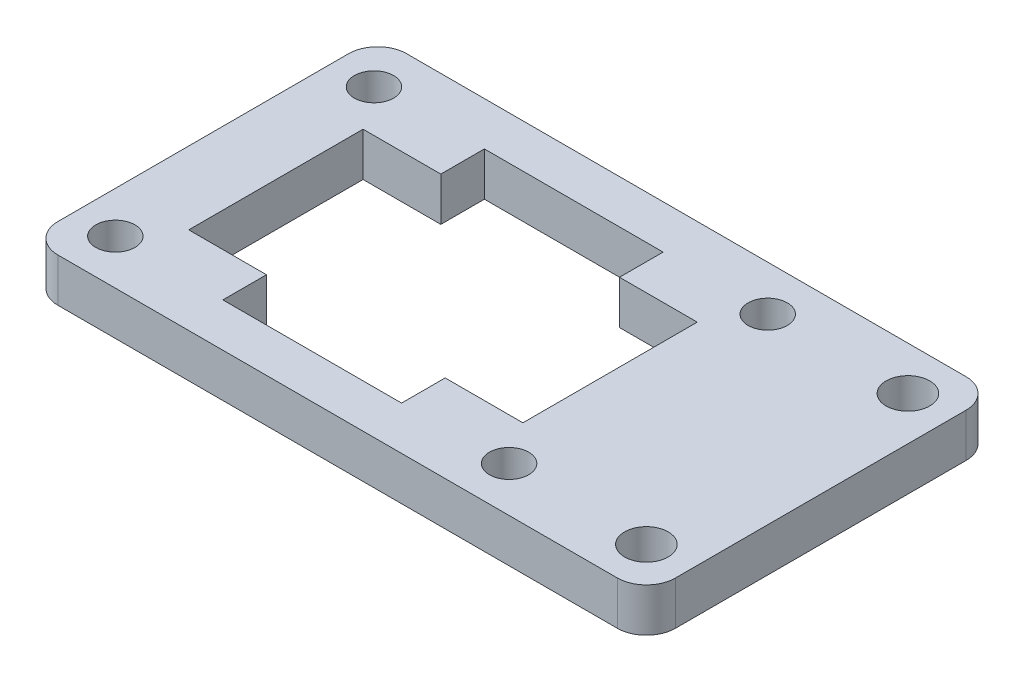
SolidWorks part; units mm, degrees
ref_plane "Front Plane" through (0, 0, 0) normal (0, 0, 1) x (1, 0, 0)
ref_plane "Top Plane" through (0, 0, 0) normal (0, 1, 0) x (1, 0, 0)
ref_plane "Right Plane" through (0, 0, 0) normal (1, 0, 0) x (0, 0, -1)
sketch "Sketch1" plane through (0, 0, 0) normal (0, 1, 0) x (1, 0, 0)
  line L0 (16.5, 21) -> (16.5, 18) construction
  line L1 (0, 0) -> (42.5, 0)
  line L2 (0, 0) -> (0, 24)
  line L3 (0, 24) -> (42.5, 24)
  line L4 (42.5, 0) -> (42.5, 24)
  line L5 (5, 18) -> (28, 18)
  line L6 (5, 18) -> (5, 6)
  line L7 (5, 6) -> (28, 6)
  line L8 (28, 18) -> (28, 6)
  line L9 (10.5, 18) -> (22.5, 18)
  line L10 (10.5, 18) -> (10.5, 21)
  line L11 (10.5, 21) -> (22.5, 21)
  line L12 (22.5, 18) -> (22.5, 21)
  line L13 (10.5, 6) -> (22.5, 6)
  line L14 (10.5, 6) -> (10.5, 3)
  line L15 (10.5, 3) -> (22.5, 3)
  line L16 (22.5, 6) -> (22.5, 3)
  circle A0 centre (2.85, 20.9) radius 1.35
  circle A1 centre (2.85, 3.1) radius 1.35
  circle A2 centre (29.95, 20.9) radius 1.35
  circle A3 centre (29.95, 3.1) radius 1.35
  circle A4 centre (39.5, 3) radius 1.5
  circle A5 centre (39.5, 21) radius 1.5
  dimension "D9" = 3
  dimension "D10" = 2.7
  dimension "D11" = 2.7
  dimension "D1" = 42.5
  dimension "D2" = 24
  dimension "D3" = 5
  dimension "D4" = 5.5
  dimension "D5" = 18
  dimension "D6" = 23
  dimension "D7" = 3
  dimension "D8" = 12
  dimension "D12" = 3
  dimension "D13" = 3.1
  dimension "D14" = 3.1
  dimension "D15" = 2.85
  dimension "D16" = 12.55
  dimension "D17" = 3
  dimension "D18" = 3
extrude "Boss-Extrude1" add sketch "Sketch1" along normal blind 3 contours L1 L4 L3 L2 A5 A4 A3 A2 A1 A0 L7 L16 L15 L14 L6 L5 L10 L11 L12 L8
sketch "Sketch2" plane through (0, 3, 0) normal (0, 1, 0) x (1, 0, 0)
  line L0 (10.5, 3) -> (22.5, 3) construction
  line L1 (22.5, 6) -> (22.65, 6)
  line L2 (22.5, 6) -> (22.5, 3)
  line L3 (22.5, 3) -> (22.65, 3)
  line L4 (22.65, 6) -> (22.65, 3)
  line L5 (10.5, 6) -> (10.35, 6)
  line L6 (10.5, 6) -> (10.5, 3)
  line L7 (10.5, 3) -> (10.35, 3)
  line L8 (10.35, 6) -> (10.35, 3)
  line L9 (10.5, 21) -> (22.5, 21) construction
  line L10 (22.5, 18) -> (22.65, 18)
  line L11 (22.5, 18) -> (22.5, 21)
  line L12 (22.5, 21) -> (22.65, 21)
  line L13 (22.65, 18) -> (22.65, 21)
  line L14 (10.5, 18) -> (10.35, 18)
  line L15 (10.5, 18) -> (10.5, 21)
  line L16 (10.5, 21) -> (10.35, 21)
  line L17 (10.35, 18) -> (10.35, 21)
  dimension "D1" = 0.15
extrude "Cut-Extrude1" cut sketch "Sketch2" against normal through all
fillet "Fillet1" radius 2 4 edges at (0, 1.5, -24) (42.5, 1.5, -24) (42.5, 1.5, 0) (0, 1.5, 0)
